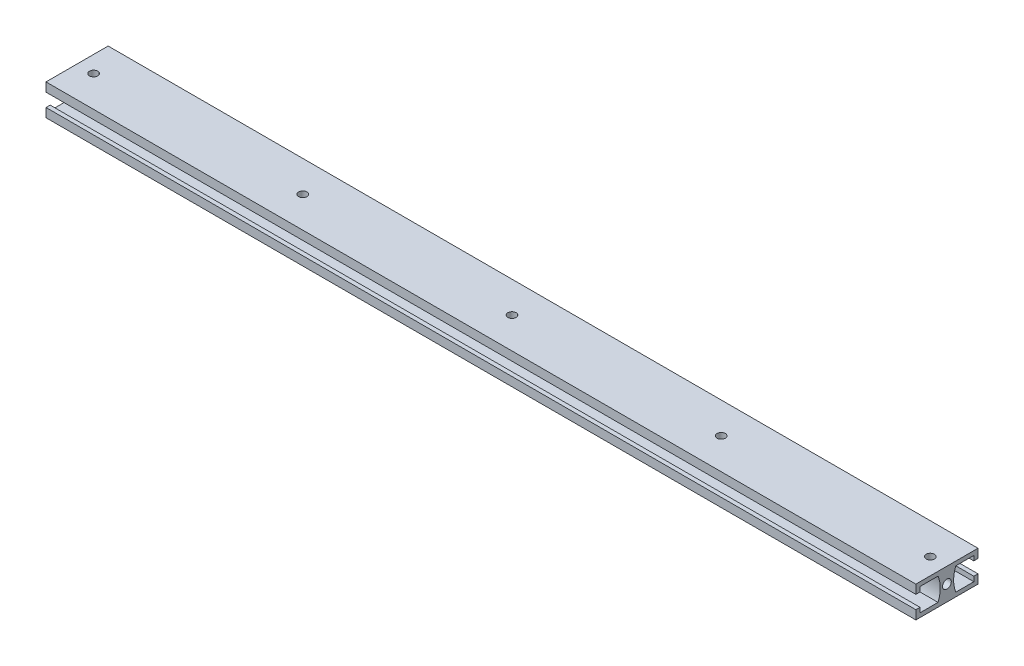
SolidWorks part; units mm, degrees
ref_plane "Front Plane" through (0, 0, 0) normal (0, 0, 1) x (1, 0, 0)
ref_plane "Top Plane" through (0, 0, 0) normal (0, 1, 0) x (1, 0, 0)
ref_plane "Right Plane" through (0, 0, 0) normal (1, 0, 0) x (0, 0, -1)
sketch "Sketch1" plane through (0, 0, 0) normal (0, 1, 0) x (1, 0, 0)
  line L0 (-2235.5671, 0) -> (109542.7862, 0) construction
  line L1 (0, -2235.5671) -> (0, 109542.7862) construction
  line L7 (-210, 15) -> (210, 15)
  line L8 (-210, 15) -> (-210, -15)
  line L25 (-210, -15) -> (210, -15)
  line L26 (210, 15) -> (210, -15)
  circle A0 centre (0, 0) radius 2
  circle A1 centre (-101, 0) radius 2
  circle A2 centre (-202, 0) radius 2
  circle A3 centre (101, 0) radius 2
  circle A4 centre (202, 0) radius 2
  point P4 (0, 0)
  point P10 (-210, 0)
  dimension "D2" = 101
  dimension "D1" = 30
  dimension "D3" = 101
  dimension "D4" = 8
  dimension "D5" = 101
  dimension "D6" = 101
  dimension "D7" = 8
extrude "Boss-Extrude1" add sketch "Sketch1" along normal blind 15
sketch "Sketch2" plane through (210, 0, 0) normal (1, 0, 0) x (0, 0, -1)
  line L0 (15, 7.5) -> (-15, 7.5) construction
  line L1 (15, 15) -> (15, 0) construction
  line L2 (-15, 15) -> (-15, 0) construction
  line L3 (0, 15) -> (0, 0) construction
  line L4 (-15, 15) -> (15, 15) construction
  line L5 (-15, 0) -> (15, 0) construction
  line L6 (15, 10.7) -> (13, 10.7)
  line L7 (15, 4.3) -> (13, 4.3)
  line L8 (-15, 4.3) -> (-13, 4.3)
  line L9 (-13, 2) -> (13, 2)
  line L10 (13, 2) -> (13, 13)
  line L11 (13, 13) -> (-13, 13)
  line L12 (-13, 13) -> (-13, 2)
  line L13 (-13, 2) -> (13, 2)
  line L14 (13, 2) -> (13, 13)
  line L15 (13, 13) -> (-13, 13)
  line L16 (-13, 13) -> (-13, 2)
  line L17 (-15, 10.7) -> (-13, 10.7)
  arc A0 (4.2849, 13) -> (4.2849, 2) centre (18.2147, 7.5) ccw
  arc A1 (-4.2849, 13) -> (-4.2849, 2) centre (-18.2147, 7.5) cw
  line M10 (15, 0) -> (15, 15)
  line M12 (-15, 15) -> (-15, 0)
  dimension "D2" = 3.2
  dimension "D3" = 3.2
  dimension "D1" = 2
extrude "Cut-Extrude1" cut sketch "Sketch2" against normal through all contours L15 A0 L13 L14 | L14 L7 L6 M10 | A1 L15 L16 L13 | L17 L8 L16 M12
hole_wizard "Tap Drill for M5x0.8 Tap1" positions "Sketch3" profile "Sketch4" hole size "M5x0.8" standard "ANSI Metric" end condition through all
sketch "Sketch3" plane through (210, 0, 0) normal (1, 0, 0) x (0, 0, -1)
  point P0 (0, 7.4992)
sketch "Sketch4" plane through (210, 7.4992, 0) normal (0, 1, 0) x (0, 0, -1)
  line L0 (0, 0) -> (0, 420)
  line L1 (0, 420) -> (2.1, 420)
  line L2 (2.1, 420) -> (2.1, 0)
  line L5 (2.1, 0) -> (0, 0)
  line L11 (0, -6.35) -> (0, 107.95) construction
  dimension "Thru Hole Dia." = 4.2
  dimension "Thru Hole Depth" = 420
